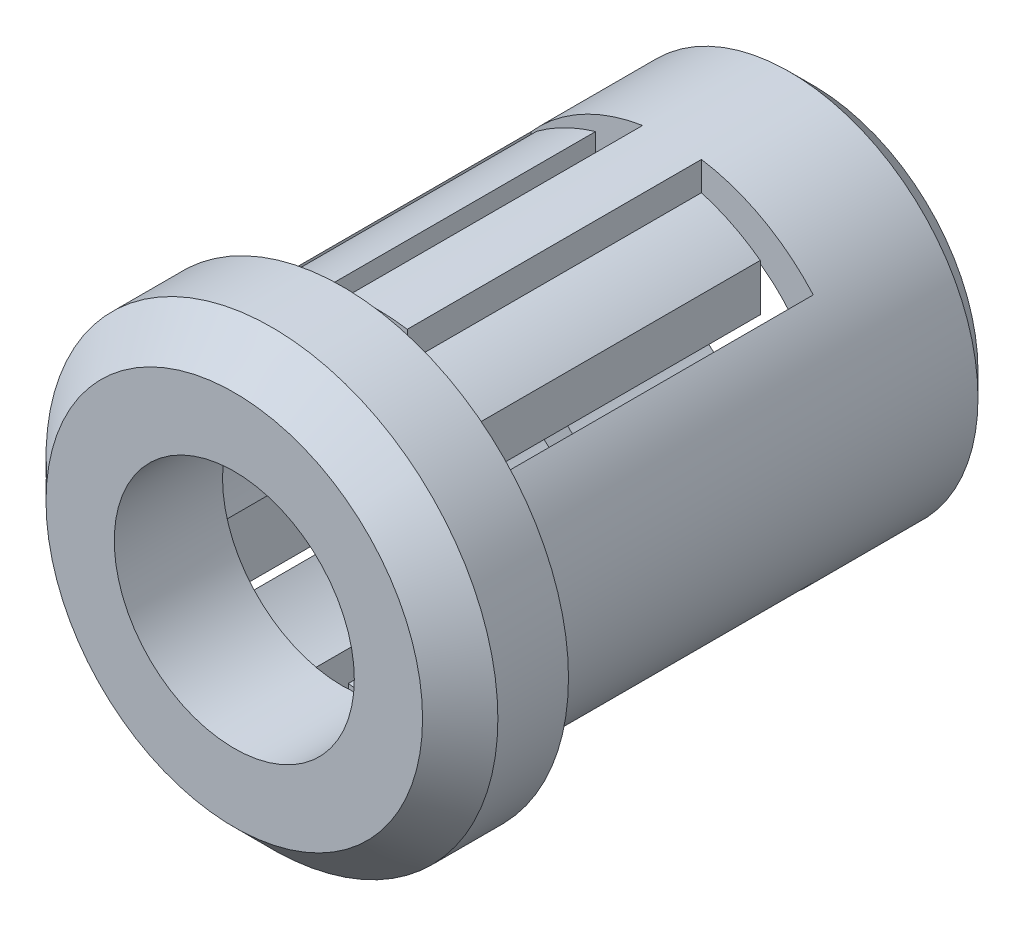
SolidWorks part; units mm, degrees
ref_plane "Front Plane" through (0, 0, 0) normal (0, 0, 1) x (1, 0, 0)
ref_plane "Top Plane" through (0, 0, 0) normal (0, 1, 0) x (1, 0, 0)
ref_plane "Right Plane" through (0, 0, 0) normal (1, 0, 0) x (0, 0, -1)
sketch "Sketch1" plane through (0, 0, 0) normal (0, 0, 1) x (1, 0, 0)
  circle A0 centre (0, 0) radius 4
  dimension "D1" = 8
extrude "Boss-Extrude1" add sketch "Sketch1" along normal blind 10
sketch "Sketch2" plane through (0, 0, 10) normal (0, 0, 1) x (1, 0, 0)
  circle A0 centre (0, 0) radius 4.8
  dimension "D1" = 9.6
extrude "Boss-Extrude2" add sketch "Sketch2" along normal blind 2.3
chamfer "Chamfer1" distance 0.8 angle 45 1 edges at (4.8, 0, 12.3)
chamfer "Chamfer2" distance 0.5 angle 45 1 edges at (4, 0, 0)
sketch "Sketch3" plane through (0, 0, 12.3) normal (0, 0, 1) x (1, 0, 0)
  circle A0 centre (0, 0) radius 2.55
  dimension "D1" = 5.1
extrude "Cut-Extrude1" cut sketch "Sketch3" against normal blind 3
sketch "Sketch4" plane through (0, 0, 0) normal (0, 0, -1) x (-1, 0, 0)
  circle A0 centre (0, 0) radius 3.25
  dimension "D1" = 6.5
extrude "Cut-Extrude2" cut sketch "Sketch4" against normal blind 10
sketch "Sketch5" plane through (0, 0, 0) normal (0, 1, 0) x (1, 0, 0)
  line L0 (0, 0) -> (0, -12.3) construction
  line L1 (3.5, 0) -> (-3.5, 0) construction
  line L2 (-4, -12.3) -> (4, -12.3) construction
  line L3 (4.8, -10) -> (-4.8, -10) construction
  line L4 (-3, -10) -> (-2.375, -10)
  line L5 (-3, -10) -> (-3, -3)
  line L6 (-3, -3) -> (-0.625, -3)
  line L7 (3, -10) -> (3, -3)
  line L8 (-1.75, -10) -> (-1.75, -3) construction
  line L9 (-1.125, -10) -> (1.125, -10)
  line L10 (-0.625, -3) -> (-0.625, -9.25)
  line L11 (-0.625, -9.25) -> (0.625, -9.25)
  line L12 (0.625, -3) -> (0.625, -9.25)
  line L13 (0.625, -3) -> (3, -3)
  line L14 (1.75, -10) -> (1.75, -3) construction
  line L15 (1.125, -10) -> (1.125, -3.5)
  line L16 (-2.375, -10) -> (-2.375, -3.5)
  line L17 (-2.375, -3.5) -> (-1.125, -3.5)
  line L18 (-1.125, -10) -> (-1.125, -3.5)
  line L19 (2.375, -3.5) -> (1.125, -3.5)
  line L20 (2.375, -10) -> (2.375, -3.5)
  line L21 (2.375, -10) -> (3, -10)
  point P17 (0, -9.25)
  point P26 (-1.75, -3.5)
  dimension "D1" = 6
  dimension "D2" = 7
  dimension "D3" = 1.25
  dimension "D4" = 0.75
  dimension "D5" = 1.75
  dimension "D6" = 1.75
  dimension "D7" = 1.25
  dimension "D8" = 6.5
extrude "Cut-Extrude3" cut sketch "Sketch5" against normal mid plane 10
